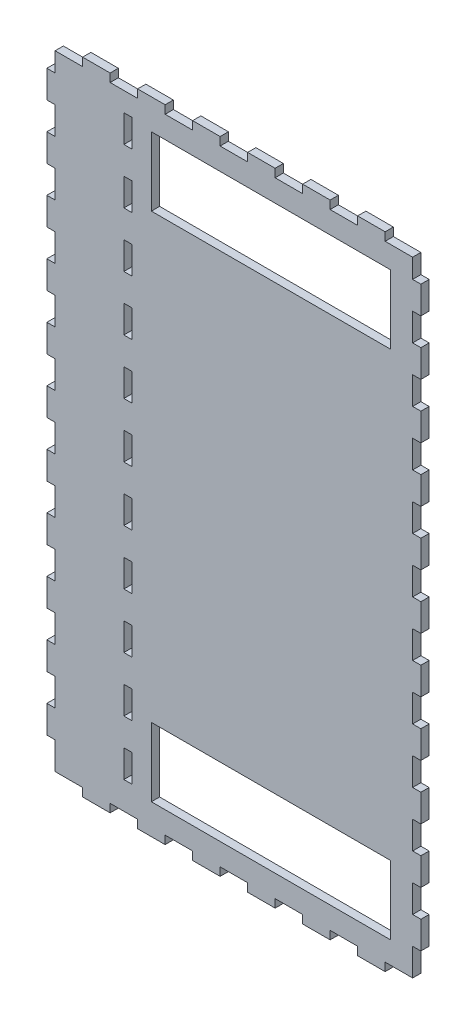
SolidWorks part; units mm, degrees
ref_plane "Front Plane" through (0, 0, 0) normal (0, 0, 1) x (1, 0, 0)
ref_plane "Top Plane" through (0, 0, 0) normal (0, 1, 0) x (1, 0, 0)
ref_plane "Right Plane" through (0, 0, 0) normal (1, 0, 0) x (0, 0, -1)
sketch "Sketch1" plane through (0, 0, 0) normal (0, 0, 1) x (1, 0, 0)
  line L0 (0, 113.5) -> (130, 113.5) construction
  line L1 (0, 0) -> (130, 0)
  line L2 (0, 0) -> (0, 227)
  line L3 (0, 227) -> (130, 227)
  line L4 (130, 0) -> (130, 227)
  line L5 (35, 8) -> (122, 8)
  line L6 (35, 8) -> (35, 33)
  line L7 (35, 33) -> (122, 33)
  line L8 (122, 8) -> (122, 33)
  line L9 (35, 194) -> (122, 194)
  line L10 (122, 219) -> (122, 194)
  line L11 (35, 219) -> (122, 219)
  line L12 (35, 219) -> (35, 194)
  dimension "D1" = 130
  dimension "D2" = 227
  dimension "D3" = 35
  dimension "D4" = 8
  dimension "D5" = 8
  dimension "D6" = 25
extrude "Boss-Extrude1" add sketch "Sketch1" along normal blind 3
sketch "Sketch2" plane through (0, 0, 0) normal (0, -1, 0) x (1, 0, 0)
  line L0 (0, 0) -> (130, 0) construction
  line L1 (10, 0) -> (20, 0)
  line L2 (10, 0) -> (10, 3)
  line L3 (10, 3) -> (20, 3)
  line L4 (20, 0) -> (20, 3)
  line L5 (0, 3) -> (130, 3) construction
  line L6 (0, 3) -> (0, 0) construction
  dimension "D1" = 10
  dimension "D2" = 10
extrude "Boss-Extrude2" add sketch "Sketch2" along normal blind 3
pattern_linear "LPattern1" count 6 spacing 20 along (1, 0, 0) of "Boss-Extrude2"
sketch "Sketch3" plane through (0, 227, 0) normal (0, 1, 0) x (1, 0, 0)
  line L0 (130, -3) -> (0, -3) construction
  line L1 (10, -3) -> (20, -3)
  line L2 (10, -3) -> (10, 0)
  line L3 (10, 0) -> (20, 0)
  line L4 (20, -3) -> (20, 0)
  line L5 (130, 0) -> (0, 0) construction
  line L6 (0, -3) -> (0, 0) construction
  dimension "D1" = 10
  dimension "D2" = 10
extrude "Boss-Extrude3" add sketch "Sketch3" along normal blind 3
pattern_linear "LPattern2" count 6 spacing 20 along (1, 0, 0) of "Boss-Extrude3"
sketch "Sketch4" plane through (130, 0, 0) normal (1, 0, 0) x (0, 0, -1)
  line L0 (-3, 0) -> (-3, 227) construction
  line L1 (-3, 10) -> (0, 10)
  line L2 (-3, 10) -> (-3, 20)
  line L3 (-3, 20) -> (0, 20)
  line L4 (0, 10) -> (0, 20)
  line L5 (0, 0) -> (0, 227) construction
  line L6 (0, 0) -> (-3, 0) construction
  dimension "D1" = 10
  dimension "D2" = 10
extrude "Boss-Extrude4" add sketch "Sketch4" along normal blind 3
pattern_linear "LPattern3" count 11 spacing 20 along (0, 1, 0) of "Boss-Extrude4"
sketch "Sketch5" plane through (0, 0, 0) normal (-1, 0, 0) x (0, 0, 1)
  line L0 (0, 227) -> (0, 0) construction
  line L1 (3, 227) -> (3, 0) construction
  line L2 (0, 10) -> (3, 10)
  line L3 (0, 10) -> (0, 20)
  line L4 (0, 20) -> (3, 20)
  line L5 (3, 10) -> (3, 20)
  line L6 (3, 0) -> (0, 0) construction
  dimension "D1" = 10
  dimension "D2" = 10
extrude "Boss-Extrude5" add sketch "Sketch5" along normal blind 3
pattern_linear "LPattern4" count 11 spacing 20 along (0, 1, 0) of "Boss-Extrude5"
sketch "Sketch6" plane through (0, 0, 3) normal (0, 0, 1) x (1, 0, 0)
  line L0 (0, 70) -> (0, 60) construction
  line L1 (25, 10) -> (28, 10)
  line L2 (25, 10) -> (25, 20)
  line L3 (25, 20) -> (28, 20)
  line L4 (28, 10) -> (28, 20)
  line L5 (20, 0) -> (30, 0) construction
  dimension "D1" = 25
  dimension "D2" = 3
  dimension "D3" = 10
  dimension "D4" = 10
extrude "Cut-Extrude1" cut sketch "Sketch6" against normal blind 3
pattern_linear "LPattern5" count 11 spacing 20 along (0, 1, 0) of "Cut-Extrude1"
